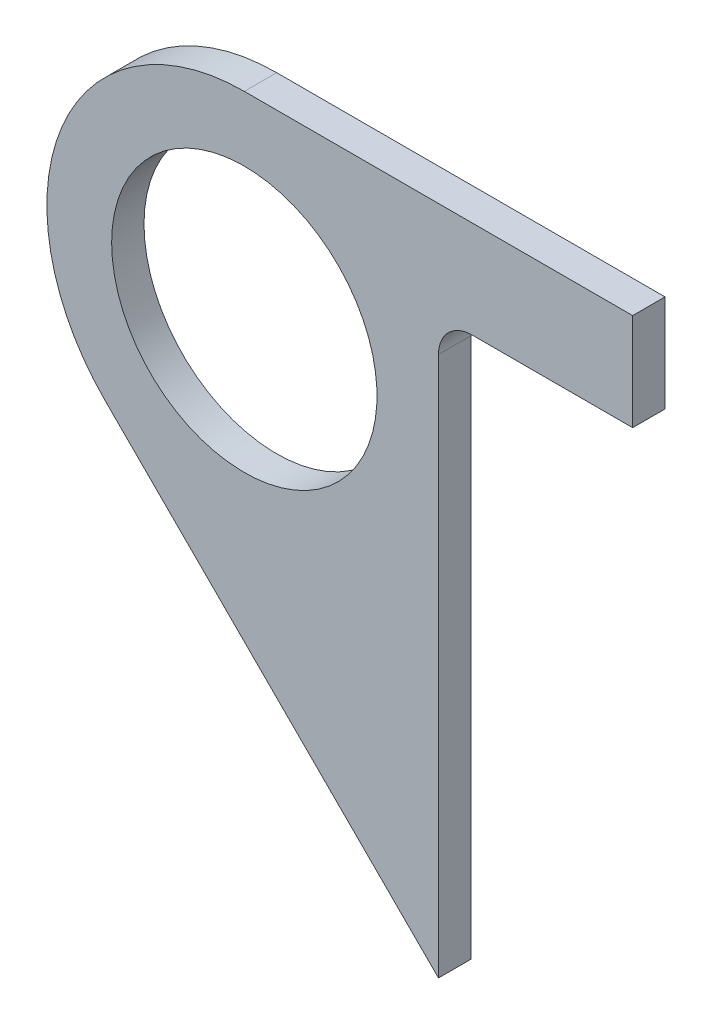
SolidWorks part; units mm, degrees
ref_plane "Front Plane" through (0, 0, 0) normal (0, 0, 1) x (1, 0, 0)
ref_plane "Top Plane" through (0, 0, 0) normal (0, 1, 0) x (1, 0, 0)
ref_plane "Right Plane" through (0, 0, 0) normal (1, 0, 0) x (0, 0, -1)
sketch "Sketch1" plane through (0, 0, 457.2) normal (0, 0, -1) x (-1, 0, 0)
  line L0 (273.05, 603.25) -> (273.05, 584.2)
  line L5 (273.05, 584.2) -> (311.15, 584.2)
  line L6 (311.15, 584.2) -> (311.15, 471.6354)
  line L8 (311.15, 471.6354) -> (376.6398, 537.1252)
  line L9 (273.05, 603.25) -> (349.25, 603.25)
  line L10 (311.15, 609.6) -> (311.15, 0) construction
  line L11 (-304.8, 603.25) -> (304.8, 603.25) construction
  arc A0 (349.25, 603.25) -> (376.6398, 537.1252) centre (349.25, 564.515) cw
  circle A1 centre (349.25, 564.515) radius 26.035
  dimension "D3" = 12.7
  dimension "D4" = 52.07
  dimension "D1" = 19.05
  dimension "D2" = 38.1
  dimension "D5" = 45
  dimension "D6" = 38.1
extrude "Boss-Extrude1" add sketch "Sketch1" along normal blind 6.35
fillet "Fillet1" radius 6.604 1 edges at (-311.15, 584.2, 454.025)
